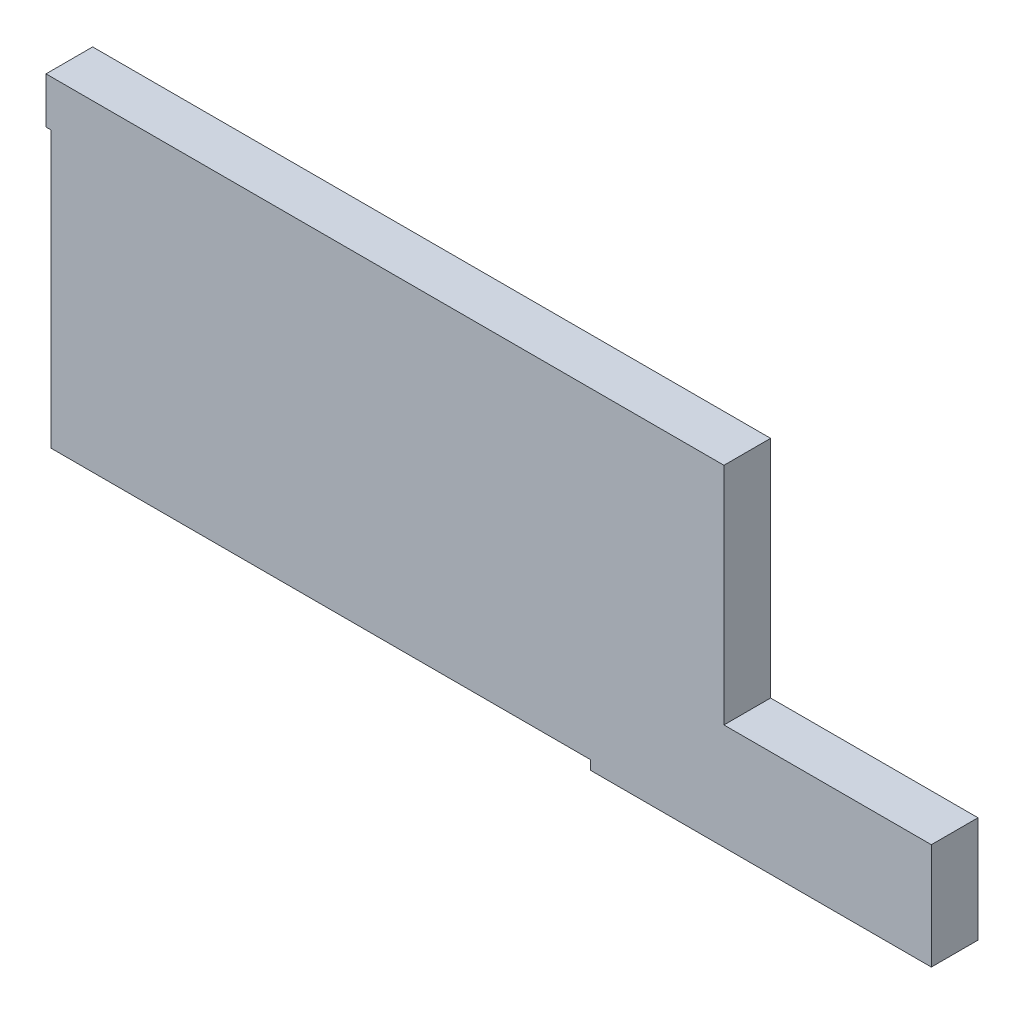
SolidWorks part; units mm, degrees
ref_plane "Front Plane" through (0, 0, 0) normal (0, 0, 1) x (1, 0, 0)
ref_plane "Top Plane" through (0, 0, 0) normal (0, 1, 0) x (1, 0, 0)
ref_plane "Right Plane" through (0, 0, 0) normal (1, 0, 0) x (0, 0, -1)
sketch "Sketch2" plane through (0, 0, 0) normal (0, 0, 1) x (1, 0, 0)
  line L20 (191, -14.196) -> (191, -37.196)
  line L21 (191, -14.196) -> (191, -37.196)
  line L22 (191, -37.196) -> (117, -37.196)
  line L23 (191, -37.196) -> (117, -37.196)
  line L24 (117, -37.196) -> (117, -35.196)
  line L25 (117, -37.196) -> (117, -35.196)
  line L26 (117, -35.196) -> (0, -35.196)
  line L27 (117, -35.196) -> (0, -35.196)
  line L28 (0, -35.196) -> (0, 24.604)
  line L29 (0, -35.196) -> (0, 24.604)
  line L30 (0, 24.604) -> (-1.1, 24.604)
  line L31 (0, 24.604) -> (-1.1, 24.604)
  line L32 (-1.1, 24.604) -> (-1.1, 34.604)
  line L33 (-1.1, 24.604) -> (-1.1, 34.604)
  line L34 (-1.1, 34.604) -> (146, 34.604)
  line L35 (-1.1, 34.604) -> (146, 34.604)
  line L36 (146, 34.604) -> (146, -14.196)
  line L37 (146, 34.604) -> (146, -14.196)
  line L38 (146, -14.196) -> (191, -14.196)
  line L39 (146, -14.196) -> (191, -14.196)
extrude "Boss-Extrude1" add sketch "Sketch2" against normal blind 10.125
